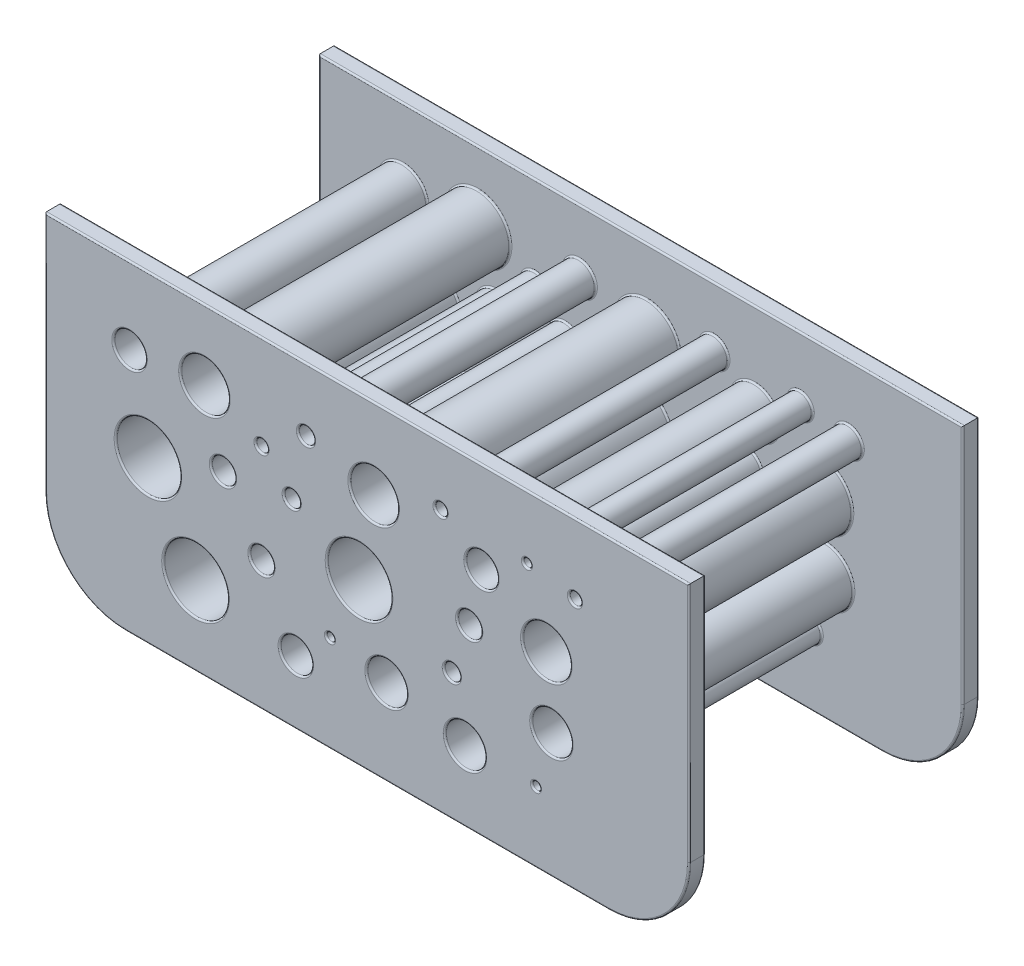
SolidWorks part; units mm, degrees
ref_plane "Ebene vorne" through (0, 0, 0) normal (0, 0, 1) x (1, 0, 0)
ref_plane "Ebene oben" through (0, 0, 0) normal (0, 1, 0) x (1, 0, 0)
ref_plane "Ebene rechts" through (0, 0, 0) normal (1, 0, 0) x (0, 0, -1)
sketch "Skizze1" plane through (0, 0, 0) normal (0, 0, 1) x (1, 0, 0)
  line L0 (-40, 0) -> (40, 0) construction
  line L1 (-40, -16) -> (40, -16) construction
  line L2 (-40, -16) -> (-40, 16) construction
  line L3 (-40, 16) -> (40, 16) construction
  line L4 (40, -16) -> (40, 16) construction
  line L5 (-40, -16) -> (40, 16) construction
  line L6 (-40, 16) -> (40, -16) construction
  circle A8 centre (-1.0033, 0) radius 4
  circle A9 centre (-1.0033, 0) radius 5
  circle A10 centre (-21.3167, -10.1981) radius 4
  circle A11 centre (-21.3167, -10.1981) radius 5
  circle A12 centre (-27.2208, 0) radius 4
  circle A13 centre (-27.2208, 0) radius 5
  circle A14 centre (22.2625, 3.8773) radius 3
  circle A15 centre (22.2625, 3.8773) radius 4
  circle A16 centre (-20.2074, 11.3186) radius 3
  circle A17 centre (-20.2074, 11.3186) radius 4
  circle A18 centre (0.8173, 10.0317) radius 3
  circle A19 centre (0.8173, 10.0317) radius 4
  circle A20 centre (22.8952, -4.5326) radius 2.5
  circle A21 centre (22.8952, -4.5326) radius 3.5
  circle A22 centre (12.1567, -11.2535) radius 2.5
  circle A23 centre (12.1567, -11.2535) radius 3.5
  circle A24 centre (2.4164, -9.3587) radius 2.5
  circle A25 centre (2.4164, -9.3587) radius 3.5
  circle A26 centre (-8.8558, -12.0817) radius 2
  circle A27 centre (-8.8558, -12.0817) radius 3
  circle A28 centre (-29.5095, 10.4796) radius 2
  circle A29 centre (-29.5095, 10.4796) radius 3
  circle A30 centre (14.2047, 8.6993) radius 2
  circle A31 centre (14.2047, 8.6993) radius 3
  circle A32 centre (12.6819, 1.9739) radius 1.5
  circle A33 centre (12.6819, 1.9739) radius 2.5
  circle A34 centre (-13.1158, -3.9759) radius 1.5
  circle A35 centre (-13.1158, -3.9759) radius 2.5
  circle A36 centre (-17.905, 3.2037) radius 1.5
  circle A37 centre (-17.905, 3.2037) radius 2.5
  circle A38 centre (10.5293, -4.2117) radius 1
  circle A39 centre (10.5293, -4.2117) radius 2
  circle A40 centre (-7.5898, 12.1889) radius 1
  circle A41 centre (-7.5898, 12.1889) radius 2
  circle A42 centre (-9.3625, 4.51) radius 1
  circle A43 centre (-9.3625, 4.51) radius 2
  circle A44 centre (-13.1158, 8.3186) radius 0.75
  circle A45 centre (-13.1158, 8.3186) radius 1.75
  circle A46 centre (9.1284, 12.6079) radius 0.75
  circle A47 centre (9.1284, 12.6079) radius 1.75
  circle A48 centre (25.8156, 11.3186) radius 0.75
  circle A49 centre (25.8156, 11.3186) radius 1.75
  circle A50 centre (19.8515, 12.1889) radius 0.5
  circle A51 centre (19.8515, 12.1889) radius 1.5
  circle A52 centre (20.9713, -11.2535) radius 0.5
  circle A53 centre (20.9713, -11.2535) radius 1.5
  circle A54 centre (-4.6129, -8.0288) radius 0.5
  circle A55 centre (-4.6129, -8.0288) radius 1.5
  point P0 (0, 0)
  dimension "D3" = 8
  dimension "D4" = 10
  dimension "D5" = 8
  dimension "D6" = 10
  dimension "D7" = 8
  dimension "D8" = 10
  dimension "D9" = 6
  dimension "D10" = 8
  dimension "D11" = 6
  dimension "D12" = 8
  dimension "D13" = 6
  dimension "D14" = 8
  dimension "D15" = 5
  dimension "D16" = 7
  dimension "D17" = 5
  dimension "D18" = 7
  dimension "D19" = 5
  dimension "D20" = 7
  dimension "D21" = 4
  dimension "D22" = 6
  dimension "D23" = 4
  dimension "D24" = 6
  dimension "D25" = 4
  dimension "D26" = 6
  dimension "D27" = 3
  dimension "D28" = 5
  dimension "D29" = 3
  dimension "D30" = 5
  dimension "D31" = 3
  dimension "D32" = 5
  dimension "D33" = 2
  dimension "D34" = 4
  dimension "D35" = 2
  dimension "D36" = 4
  dimension "D37" = 2
  dimension "D38" = 4
  dimension "D39" = 1.5
  dimension "D40" = 3.5
  dimension "D41" = 1.5
  dimension "D42" = 3.5
  dimension "D43" = 1.5
  dimension "D44" = 3.5
  dimension "D45" = 1
  dimension "D46" = 3
  dimension "D47" = 1
  dimension "D48" = 3
  dimension "D49" = 1
  dimension "D50" = 3
  dimension "D1" = 32
  dimension "D2" = 80
extrude "Aufsatz-Linear austragen1" add sketch "Skizze1" along normal mid plane 32
sketch "Skizze2" plane through (0, 0, 16) normal (0, 0, 1) x (1, 0, 0)
  line L1 (-40, -20) -> (40, -20)
  line L2 (-40, -20) -> (-40, 20)
  line L3 (-40, 20) -> (40, 20)
  line L4 (40, -20) -> (40, 20)
  line L5 (-40, -20) -> (40, 20) construction
  line L6 (-40, 20) -> (40, -20) construction
  point P0 (0, 0)
  dimension "D1" = 80
  dimension "D2" = 40
extrude "Aufsatz-Linear austragen2" add sketch "Skizze2" along normal blind 2
sketch "Skizze3" plane through (0, 0, -16) normal (0, 0, -1) x (-1, 0, 0)
  circle A0 centre (-25.8156, 11.3186) radius 0.75
  circle A1 centre (-19.8515, 12.1889) radius 0.5
  circle A2 centre (-9.1284, 12.6079) radius 0.75
  circle A4 centre (-14.2047, 8.6993) radius 2
  circle A5 centre (-22.2625, 3.8773) radius 3
  circle A6 centre (-22.8952, -4.5326) radius 2.5
  circle A7 centre (-20.9713, -11.2535) radius 0.5
  circle A8 centre (-12.1567, -11.2535) radius 2.5
  circle A9 centre (-10.5293, -4.2117) radius 1
  circle A10 centre (-12.6819, 1.9739) radius 1.5
  circle A11 centre (1.0033, 0) radius 4
  circle A12 centre (-2.4164, -9.3587) radius 2.5
  circle A13 centre (4.6129, -8.0288) radius 0.5
  circle A14 centre (8.8558, -12.0817) radius 2
  circle A15 centre (21.3167, -10.1981) radius 4
  circle A16 centre (13.1158, -3.9759) radius 1.5
  circle A17 centre (27.2208, 0) radius 4
  circle A18 centre (17.905, 3.2037) radius 1.5
  circle A19 centre (9.3625, 4.51) radius 1
  circle A20 centre (13.1158, 8.3186) radius 0.75
  circle A21 centre (7.5898, 12.1889) radius 1
  circle A22 centre (-0.8173, 10.0317) radius 3
  circle A23 centre (20.2074, 11.3186) radius 3
  circle A24 centre (29.5095, 10.4796) radius 2
extrude "Schnitt-Linear austragen1" cut sketch "Skizze3" against normal through all and the other way through all
sketch "Skizze4" plane through (0, 0, -16) normal (0, 0, -1) x (-1, 0, 0)
  line L1 (-40, -20) -> (40, -20)
  line L2 (-40, -20) -> (-40, 20)
  line L3 (-40, 20) -> (40, 20)
  line L4 (40, -20) -> (40, 20)
  line L5 (-40, -20) -> (40, 20) construction
  line L6 (-40, 20) -> (40, -20) construction
  point P0 (0, 0)
extrude "Aufsatz-Linear austragen3" add sketch "Skizze4" along normal blind 2
sketch "Skizze5" plane through (0, 0, 18) normal (0, 0, 1) x (1, 0, 0)
  circle A0 centre (-29.5095, 10.4796) radius 2
  circle A1 centre (-20.2074, 11.3186) radius 3
  circle A2 centre (-27.2208, 0) radius 4
  circle A3 centre (-21.3167, -10.1981) radius 4
  circle A4 centre (-17.905, 3.2037) radius 1.5
  circle A5 centre (-13.1158, -3.9759) radius 1.5
  circle A6 centre (-8.8558, -12.0817) radius 2
  circle A7 centre (-1.0033, 0) radius 4
  circle A8 centre (-9.3625, 4.51) radius 1
  circle A9 centre (-13.1158, 8.3186) radius 0.75
  circle A10 centre (-7.5898, 12.1889) radius 1
  circle A11 centre (0.8173, 10.0317) radius 3
  circle A12 centre (9.1284, 12.6079) radius 0.75
  circle A13 centre (14.2047, 8.6993) radius 2
  circle A14 centre (12.6819, 1.9739) radius 1.5
  circle A15 centre (-4.6129, -8.0288) radius 0.5
  circle A16 centre (2.4164, -9.3587) radius 2.5
  circle A17 centre (10.5293, -4.2117) radius 1
  circle A18 centre (12.1567, -11.2535) radius 2.5
  circle A19 centre (20.9713, -11.2535) radius 0.5
  circle A20 centre (22.8952, -4.5326) radius 2.5
  circle A21 centre (22.2625, 3.8773) radius 3
  circle A22 centre (25.8156, 11.3186) radius 0.75
  circle A23 centre (19.8515, 12.1889) radius 0.5
extrude "Schnitt-Linear austragen2" cut sketch "Skizze5" against normal through all and the other way through all
fillet "Verrundung1" radius 10 4 edges at (-40, -20, 17) (-40, -20, -17) (40, -20, -17) (40, -20, 17)
fillet "Verrundung2" radius 0.2 120 edges at (37.0711, -17.0711, 16) (40, 5, 16) (0, 20, 16) (-40, 5, 16) (-37.0711, -17.0711, 16) (0, -20, 16) (3.9967, 0, 16) (-16.3167, -10.1981, 16) (-22.2208, 0, 16) (26.2625, 3.8773, 16) (-16.2074, 11.3186, 16) (4.8173, 10.0317, 16) (26.3952, -4.5326, 16) (15.6567, -11.2535, 16) (5.9164, -9.3587, 16) (-5.8558, -12.0817, 16) (-26.5095, 10.4796, 16) (17.2047, 8.6993, 16) (15.1819, 1.9739, 16) (-10.6158, -3.9759, 16) (-15.405, 3.2037, 16) (12.5293, -4.2117, 16) (-5.5898, 12.1889, 16) (-7.3625, 4.51, 16) (-11.3658, 8.3186, 16) (10.8784, 12.6079, 16) (27.5656, 11.3186, 16) (21.3515, 12.1889, 16) (22.4713, -11.2535, 16) (-3.1129, -8.0288, 16) (0, 20, -16) (40, 5, -16) (37.0711, -17.0711, -16) (0, -20, -16) (-37.0711, -17.0711, -16) (-40, 5, -16) (-3.1129, -8.0288, -16) (22.4713, -11.2535, -16) (21.3515, 12.1889, -16) (27.5656, 11.3186, -16) (10.8784, 12.6079, -16) (-11.3658, 8.3186, -16) (-7.3625, 4.51, -16) (-5.5898, 12.1889, -16) (12.5293, -4.2117, -16) (-15.405, 3.2037, -16) (-10.6158, -3.9759, -16) (15.1819, 1.9739, -16) (17.2047, 8.6993, -16) (-26.5095, 10.4796, -16) (-5.8558, -12.0817, -16) (5.9164, -9.3587, -16) (15.6567, -11.2535, -16) (26.3952, -4.5326, -16) (4.8173, 10.0317, -16) (-16.2074, 11.3186, -16) (26.2625, 3.8773, -16) (-22.2208, 0, -16) (-16.3167, -10.1981, -16) (3.9967, 0, -16) (37.0711, -17.0711, -18) (40, 5, -18) (0, 20, -18) (-40, 5, -18) (-37.0711, -17.0711, -18) (0, -20, -18) (-27.5095, 10.4796, -18) (25.2625, 3.8773, -18) (26.5656, 11.3186, -18) (20.3515, 12.1889, -18) (25.3952, -4.5326, -18) (21.4713, -11.2535, -18) (14.6567, -11.2535, -18) (11.5293, -4.2117, -18) (-16.405, 3.2037, -18) (-17.3167, -10.1981, -18) (-23.2208, 0, -18) (-17.2074, 11.3186, -18) (-8.3625, 4.51, -18) (2.9967, 0, -18) (-6.8558, -12.0817, -18) (-11.6158, -3.9759, -18) (4.9164, -9.3587, -18) (-4.1129, -8.0288, -18) (14.1819, 1.9739, -18) (16.2047, 8.6993, -18) (9.8784, 12.6079, -18) (3.8173, 10.0317, -18) (-6.5898, 12.1889, -18) (-12.3658, 8.3186, -18) (0, 20, 18) (40, 5, 18) (37.0711, -17.0711, 18) (0, -20, 18) (-37.0711, -17.0711, 18) (-40, 5, 18) (25.0656, 11.3186, 18) (-19.405, 3.2037, 18) (-10.3625, 4.51, 18) (-13.8658, 8.3186, 18) (-8.5898, 12.1889, 18) (-2.1827, 10.0317, 18) (-23.2074, 11.3186, 18) (-31.5095, 10.4796, 18) (19.3515, 12.1889, 18) (8.3784, 12.6079, 18) (12.2047, 8.6993, 18) (19.2625, 3.8773, 18) (20.3952, -4.5326, 18) (20.4713, -11.2535, 18) (9.6567, -11.2535, 18) (9.5293, -4.2117, 18) (11.1819, 1.9739, 18) (-5.0033, 0, 18) (-0.0836, -9.3587, 18) (-5.1129, -8.0288, 18) (-10.8558, -12.0817, 18) (-25.3167, -10.1981, 18) (-14.6158, -3.9759, 18) (-31.2208, 0, 18)
